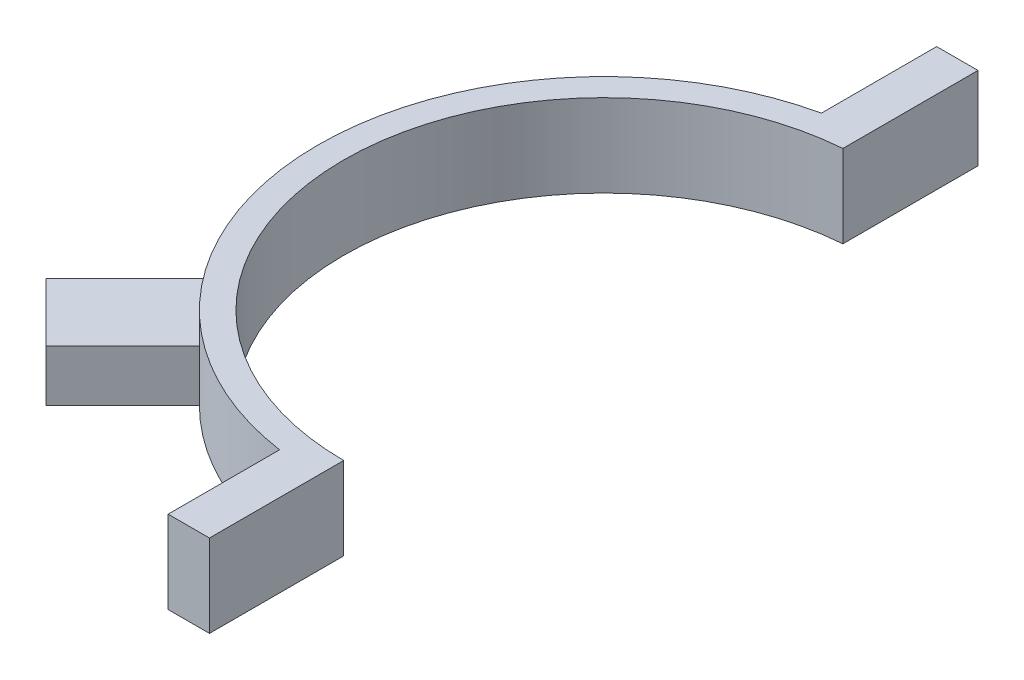
SolidWorks part; units mm, degrees
ref_plane "Front Plane" through (0, 0, 0) normal (0, 0, 1) x (1, 0, 0)
ref_plane "Top Plane" through (0, 0, 0) normal (0, 1, 0) x (1, 0, 0)
ref_plane "Right Plane" through (0, 0, 0) normal (1, 0, 0) x (0, 0, -1)
sketch "Sketch1" plane through (0, 0, 0) normal (0, 1, 0) x (1, 0, 0)
  line L0 (0, -41.9629) -> (0, 37.9148) construction
  line L6 (0, -32.004) -> (0, -35.179)
  line L7 (0, -32.004) -> (0, -35.179) construction
  line L8 (-2.54, 31.903) -> (-2.54, 35.0872)
  arc A0 (-2.54, 31.903) -> (0, -32.004) centre (0, 0) ccw
  arc A1 (-2.54, 35.0872) -> (0, -35.179) centre (0, 0) ccw
  point P4 (0, 0)
  point P8 (-2.54, 35.0872)
  point P9 (-2.54, 31.903)
  point P11 (-2.54, 35.0872)
  point P12 (0, 0)
  dimension "D1" = 64.008
  dimension "D3" = 70.358
  dimension "D4" = 2.54
extrude "Boss-Extrude1" add sketch "Sketch1" along normal blind 10.16
ref_plane "Plane1" through (0, 0, 32.004) normal (0, 0, -1) x (0, -1, 0)
sketch "Sketch3" plane through (0, 0, 32.004) normal (0, 0, -1) x (0, -1, 0)
  line L0 (-10.16, 0) -> (0, 0) construction
  line L1 (-10.16, 5.08) -> (0, 5.08)
  line L2 (-10.16, 5.08) -> (-10.16, 0)
  line L3 (-10.16, 0) -> (0, 0)
  line L4 (0, 5.08) -> (0, 0)
  line L5 (-10.16, 5.08) -> (0, 0) construction
  line L6 (-10.16, 0) -> (0, 5.08) construction
  point P0 (-5.08, 2.54)
  point P7 (0, 0)
  point P9 (0, 0)
  dimension "D1" = 5.08
  dimension "D2" = 10.16
extrude "Boss-Extrude2" add sketch "Sketch3" against normal blind 16.51
ref_plane "Plane2" through (0, 0, -32.004) normal (0, 0, 1) x (0, -1, 0)
sketch "Sketch4" plane through (0, 0, -32.004) normal (0, 0, 1) x (0, -1, 0)
  line L0 (-10.16, -2.54) -> (0, -2.54) construction
  line L1 (-10.16, -2.54) -> (0, -2.54)
  line L2 (-10.16, -2.54) -> (-10.16, -7.62)
  line L3 (-10.16, -7.62) -> (0, -7.62)
  line L4 (0, -2.54) -> (0, -7.62)
  line L5 (-10.16, -2.54) -> (0, -7.62) construction
  line L6 (-10.16, -7.62) -> (0, -2.54) construction
  point P0 (-5.08, -5.08)
  point P7 (0, 0)
  dimension "D1" = 10.16
  dimension "D2" = 5.08
extrude "Boss-Extrude3" add sketch "Sketch4" against normal blind 16.51
sketch "Sketch6" plane through (0, 0, 0) normal (0, -1, 0) x (1, 0, 0)
  line L0 (0, 0) -> (0, 53.5637) construction
  line L1 (0, 0) -> (-35.4288, 35.4288) construction
  line L2 (-22.6302, 22.6302) -> (-34.3046, 34.3046)
  line L3 (-22.6302, 22.6302) -> (-29.8145, 15.446)
  line L4 (-34.3046, 34.3046) -> (-41.4888, 27.1204)
  line L5 (-41.4888, 27.1204) -> (-29.8145, 15.446)
  arc A0 (0, 32.004) -> (-2.54, -31.903) centre (0, 0) ccw construction
  point P3 (0, 0)
  dimension "D1" = 45
  dimension "D2" = 16.51
  dimension "D3" = 10.16
extrude "Boss-Extrude5" add sketch "Sketch6" against normal blind 6.35 contours L5 L3 L2 L4
